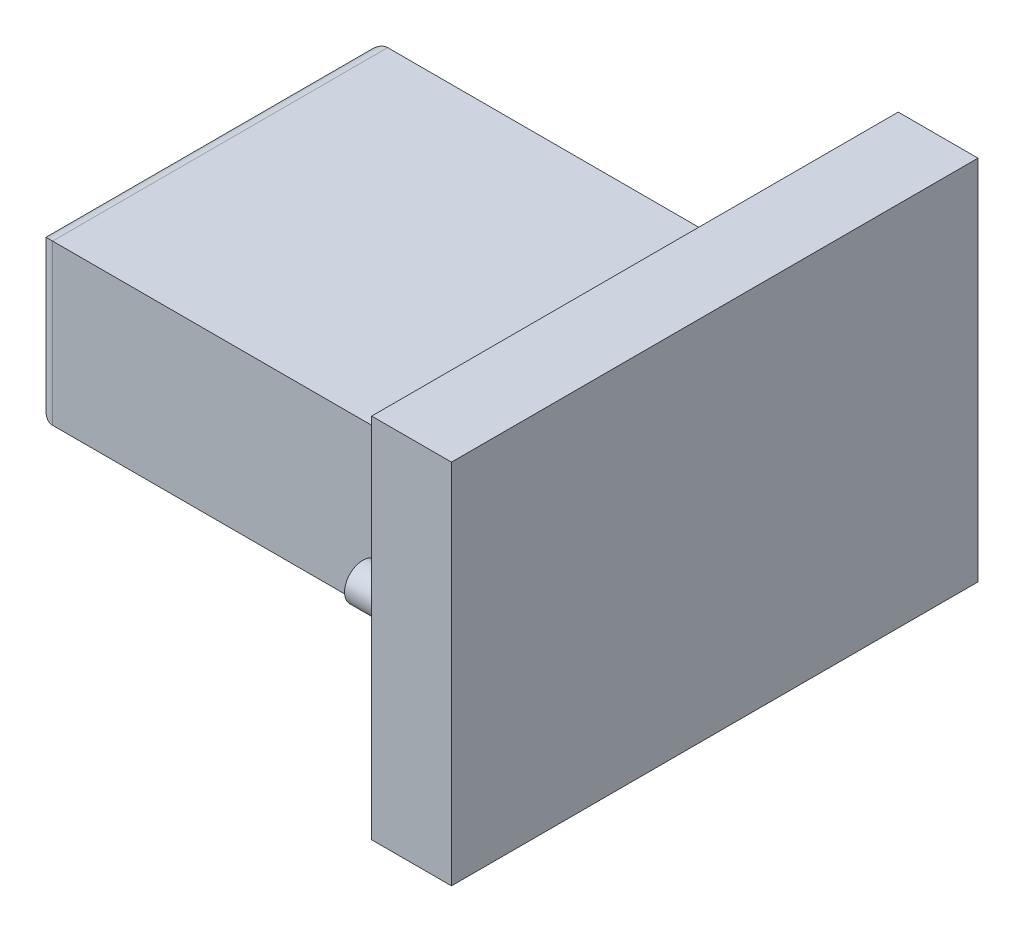
SolidWorks part; units mm, degrees
ref_plane "Front Plane" through (0, 0, 0) normal (0, 0, 1) x (1, 0, 0)
ref_plane "Top Plane" through (0, 0, 0) normal (0, 1, 0) x (1, 0, 0)
ref_plane "Right Plane" through (0, 0, 0) normal (1, 0, 0) x (0, 0, -1)
sketch "Sketch1" plane through (0, 0, 0) normal (1, 0, 0) x (0, 0, -1)
  line L1 (0, 0) -> (33, 0)
  line L2 (0, 0) -> (0, 23)
  line L3 (0, 23) -> (33, 23)
  line L4 (33, 0) -> (33, 23)
extrude "Boss-Extrude1" add sketch "Sketch1" along normal blind 5
sketch "Sketch2" plane through (0, 0, 0) normal (-1, 0, 0) x (0, 0, 1)
  line L1 (-27, 6.5) -> (-6, 6.5)
  line L2 (-27, 6.5) -> (-27, 16.5)
  line L3 (-27, 16.5) -> (-6, 16.5)
  line L4 (-6, 6.5) -> (-6, 16.5)
extrude "Boss-Extrude2" add sketch "Sketch2" along normal blind 27
fillet "Fillet1" radius 1 4 edges at (-27, 16.5, -16.5) (-27, 11.5, -6) (-27, 6.5, -16.5) (-27, 11.5, -27)
sketch "Sketch3" plane through (0, 0, 0) normal (-1, 0, 0) x (0, 0, 1)
  circle A0 centre (-2.25, 11.5) radius 1.15
  circle A1 centre (-30.75, 11.5) radius 1.15
  point P4 (0, 0)
extrude "Boss-Extrude5" add sketch "Sketch3" along normal blind 2.8
fillet "Fillet9" radius 0.25 2 edges at (0, 11.5, -29.6) (0, 11.5, -1.1)
